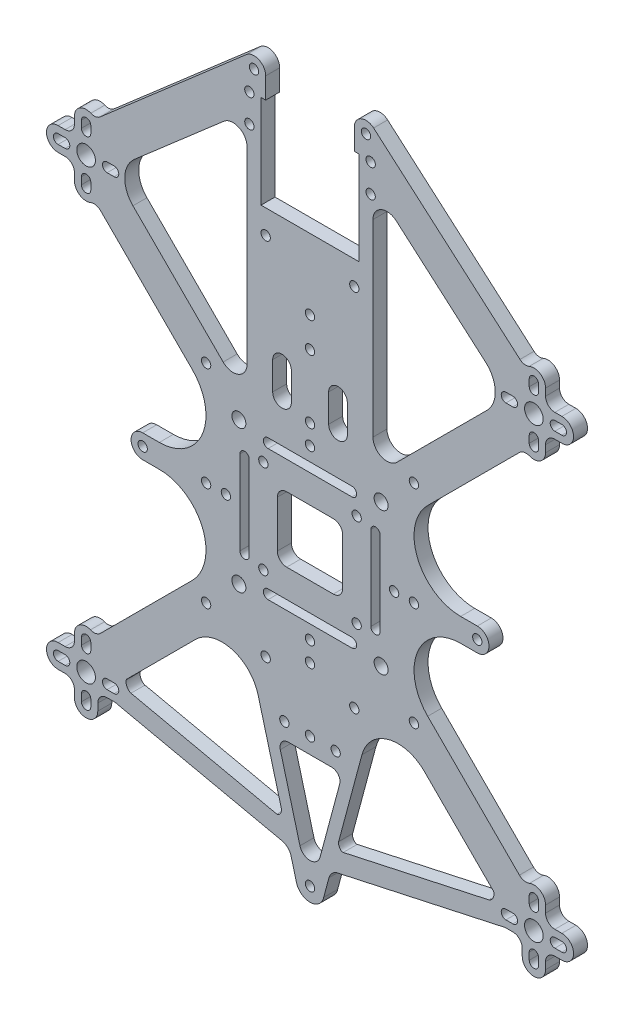
SolidWorks part; units mm, degrees
ref_plane "前视基准面" through (0, 0, 0) normal (0, 0, 1) x (1, 0, 0)
ref_plane "上视基准面" through (0, 0, 0) normal (0, 1, 0) x (1, 0, 0)
ref_plane "右视基准面" through (0, 0, 0) normal (1, 0, 0) x (0, 0, -1)
sketch "Model" plane through (0, 0, 0) normal (0, 0, 1) x (1, 0, 0)
  line L0 (38.9722, 86.626) -> (42.5374, 86.626)
  line L1 (49.6078, 103.6978) -> (29.9424, 123.3592)
  line L2 (37.1859, 136.508) -> (56.373, 153.1829)
  line L3 (61.3409, 150.9185) -> (61.3409, 110.5212)
  line L4 (56.2198, 108.3997) -> (36.8794, 127.7362)
  line L5 (27.8409, 136.6164) -> (27.8409, 138.1164)
  line L6 (25.8409, 138.1164) -> (25.8409, 136.6164)
  line L7 (27.8409, 127.6164) -> (27.8409, 126.1164)
  line L8 (25.8409, 126.1164) -> (25.8409, 127.6164)
  line L9 (22.3409, 133.1164) -> (20.8409, 133.1164)
  line L10 (20.8409, 131.1164) -> (22.3409, 131.1164)
  line L11 (31.3409, 133.1164) -> (32.8409, 133.1164)
  line L12 (32.8409, 131.1164) -> (31.3409, 131.1164)
  line L13 (24.3409, 126.1164) -> (24.3409, 127.6164)
  line L14 (22.3409, 129.6164) -> (20.8409, 129.6164)
  line L15 (20.8409, 134.6164) -> (22.3409, 134.6164)
  line L16 (24.3409, 136.6164) -> (24.3409, 138.1164)
  line L17 (27.8409, 31.6356) -> (27.8409, 30.1356)
  line L18 (25.8409, 30.1356) -> (25.8409, 31.6356)
  line L19 (27.8409, 40.6356) -> (27.8409, 42.1356)
  line L20 (25.8409, 42.1356) -> (25.8409, 40.6356)
  line L21 (22.3409, 35.1356) -> (20.8409, 35.1356)
  line L22 (20.8409, 37.1356) -> (22.3409, 37.1356)
  line L23 (31.3409, 35.1356) -> (32.8409, 35.1356)
  line L24 (32.8409, 37.1356) -> (31.3409, 37.1356)
  line L25 (121.8409, 31.6356) -> (121.8409, 30.1356)
  line L26 (123.8409, 30.1356) -> (123.8409, 31.6356)
  line L27 (121.8409, 40.6356) -> (121.8409, 42.1356)
  line L28 (123.8409, 42.1356) -> (123.8409, 40.6356)
  line L29 (127.3409, 35.1356) -> (128.8409, 35.1356)
  line L30 (128.8409, 37.1356) -> (127.3409, 37.1356)
  line L31 (118.3409, 35.1356) -> (116.8409, 35.1356)
  line L32 (116.8409, 37.1356) -> (118.3409, 37.1356)
  line L33 (125.3409, 42.1356) -> (125.3409, 40.6356)
  line L34 (127.3409, 38.6356) -> (128.8409, 38.6356)
  line L35 (128.8409, 33.6356) -> (127.3409, 33.6356)
  line L36 (125.3409, 31.6356) -> (125.3409, 30.1356)
  line L37 (120.3409, 30.1356) -> (120.3409, 31.6356)
  line L38 (118.3409, 33.6356) -> (116.8409, 33.6356)
  line L39 (65.3409, 166.0907) -> (65.3409, 161.5907)
  line L40 (65.3409, 161.5907) -> (64.3409, 161.5907)
  line L41 (64.3409, 161.5907) -> (64.3409, 141.5907)
  line L42 (64.3409, 141.5907) -> (74.8409, 141.5907)
  line L43 (29.8244, 140.7093) -> (61.2009, 167.9777)
  line L44 (84.3409, 166.0907) -> (84.3409, 161.5907)
  line L45 (84.3409, 161.5907) -> (85.3409, 161.5907)
  line L46 (85.3409, 161.5907) -> (85.3409, 141.5907)
  line L47 (85.3409, 141.5907) -> (74.8409, 141.5907)
  line L48 (114.0826, 39.2358) -> (99.3617, 53.9538)
  line L49 (85.978, 50.3669) -> (80.98, 31.728)
  line L50 (81.2114, 42.5628) -> (76.9926, 26.8183)
  line L51 (72.6891, 26.8183) -> (68.4704, 42.5628)
  line L52 (70.1918, 44.8062) -> (79.4899, 44.8062)
  line L53 (110.7096, 81.626) -> (107.1443, 81.626)
  line L54 (100.074, 64.5542) -> (119.7393, 44.8928)
  line L55 (110.7096, 86.626) -> (107.1443, 86.626)
  line L56 (100.074, 103.6978) -> (119.7393, 123.3592)
  line L57 (121.8409, 136.6164) -> (121.8409, 138.1164)
  line L58 (123.8409, 138.1164) -> (123.8409, 136.6164)
  line L59 (121.8409, 127.6164) -> (121.8409, 126.1164)
  line L60 (123.8409, 126.1164) -> (123.8409, 127.6164)
  line L61 (127.3409, 133.1164) -> (128.8409, 133.1164)
  line L62 (128.8409, 131.1164) -> (127.3409, 131.1164)
  line L63 (118.3409, 133.1164) -> (116.8409, 133.1164)
  line L64 (116.8409, 131.1164) -> (118.3409, 131.1164)
  line L65 (125.3409, 126.1164) -> (125.3409, 127.6164)
  line L66 (127.3409, 129.6164) -> (128.8409, 129.6164)
  line L67 (128.8409, 134.6164) -> (127.3409, 134.6164)
  line L68 (125.3409, 136.6164) -> (125.3409, 138.1164)
  line L69 (119.8573, 140.7093) -> (88.4808, 167.9777)
  line L70 (112.4959, 136.508) -> (93.3088, 153.1829)
  line L71 (88.3409, 150.9185) -> (88.3409, 110.5212)
  line L72 (93.462, 108.3997) -> (112.8023, 127.7362)
  line L73 (61.8096, 93.126) -> (61.8096, 75.126)
  line L74 (59.8096, 75.126) -> (59.8096, 93.126)
  line L75 (69.8409, 91.126) -> (79.8409, 91.126)
  line L76 (81.8409, 89.126) -> (81.8409, 79.126)
  line L77 (79.8409, 77.126) -> (69.8409, 77.126)
  line L78 (67.8409, 79.126) -> (67.8409, 89.126)
  line L79 (87.8721, 93.126) -> (87.8721, 75.126)
  line L80 (89.8721, 75.126) -> (89.8721, 93.126)
  line L81 (65.8409, 71.0948) -> (83.8409, 71.0948)
  line L82 (83.8409, 69.0948) -> (65.8409, 69.0948)
  line L83 (65.8409, 97.1572) -> (83.8409, 97.1572)
  line L84 (83.8409, 99.1572) -> (65.8409, 99.1572)
  line L85 (70.8409, 114.1572) -> (70.8409, 108.1572)
  line L86 (66.8409, 108.1572) -> (66.8409, 114.1572)
  line L87 (78.8409, 114.1572) -> (78.8409, 108.1572)
  line L88 (82.8409, 108.1572) -> (82.8409, 114.1572)
  line L89 (80.7239, 25.7968) -> (115.3738, 33.3482)
  line L90 (77.7722, 19.7649) -> (78.9081, 24.001)
  line L91 (81.9571, 30.2136) -> (113.2232, 37.0275)
  line L92 (24.3409, 42.1356) -> (24.3409, 40.6356)
  line L93 (22.3409, 38.6356) -> (20.8409, 38.6356)
  line L94 (20.8409, 33.6356) -> (22.3409, 33.6356)
  line L95 (24.3409, 31.6356) -> (24.3409, 30.1356)
  line L96 (29.3409, 30.1356) -> (29.3409, 31.6356)
  line L97 (31.3409, 33.6356) -> (32.8409, 33.6356)
  line L98 (68.9578, 25.7968) -> (34.3079, 33.3482)
  line L99 (71.926, 19.6934) -> (70.7737, 24.001)
  line L100 (38.9722, 81.626) -> (42.5374, 81.626)
  line L101 (49.6078, 64.5542) -> (29.9424, 44.8928)
  line L102 (35.5991, 39.2358) -> (50.32, 53.9538)
  line L103 (63.7037, 50.3669) -> (68.7017, 31.728)
  line L104 (67.7246, 30.2136) -> (36.4585, 37.0275)
  circle A0 centre (97.1147, 106.3999) radius 1
  circle A1 centre (52.567, 106.3999) radius 1
  circle A2 centre (52.567, 61.8522) radius 1
  circle A3 centre (97.1147, 61.8522) radius 1
  circle A4 centre (97.1147, 84.126) radius 1
  circle A5 centre (74.8409, 106.3999) radius 1
  circle A6 centre (52.567, 84.126) radius 1
  circle A7 centre (74.8409, 61.8522) radius 1
  circle A8 centre (64.8409, 94.126) radius 1
  circle A9 centre (84.8409, 94.126) radius 1
  circle A10 centre (64.8409, 74.126) radius 1
  circle A11 centre (84.8409, 74.126) radius 1
  circle A12 centre (26.8409, 132.1164) radius 2
  circle A13 centre (74.8409, 102.1572) radius 1
  circle A14 centre (92.8721, 84.126) radius 1
  circle A15 centre (74.8409, 66.0948) radius 1
  circle A16 centre (56.8096, 84.126) radius 1
  arc A17 (110.7096, 81.626) -> (110.7096, 86.626) centre (110.7096, 84.126) ccw
  circle A18 centre (110.7096, 84.126) radius 1
  arc A19 (38.9722, 86.626) -> (38.9722, 81.626) centre (38.9722, 84.126) ccw
  circle A20 centre (38.9722, 84.126) radius 1
  circle A21 centre (74.8409, 120.0231) radius 1
  circle A22 centre (74.8409, 48.229) radius 1
  circle A23 centre (26.8409, 36.1356) radius 2
  circle A24 centre (122.8409, 36.1356) radius 2
  arc A25 (65.3409, 166.0907) -> (61.2009, 167.9777) centre (62.8409, 166.0907) ccw
  circle A26 centre (62.8409, 166.0907) radius 1
  arc A27 (88.4808, 167.9777) -> (84.3409, 166.0907) centre (86.8409, 166.0907) ccw
  circle A28 centre (86.8409, 166.0907) radius 1
  circle A29 centre (74.8409, 20.4032) radius 1
  arc A30 (71.926, 19.6934) -> (77.7722, 19.7649) centre (74.8409, 20.4032) ccw
  arc A31 (119.7393, 44.8928) -> (121.9034, 44.4531) centre (121.1534, 46.3072) ccw
  arc A32 (27.7784, 44.4531) -> (29.9424, 44.8928) centre (28.5284, 46.3072) ccw
  arc A33 (29.9424, 123.3592) -> (27.7784, 123.7989) centre (28.5284, 121.9448) ccw
  arc A34 (27.843, 140.4068) -> (29.8244, 140.7093) centre (28.5945, 142.1245) ccw
  arc A35 (37.1859, 136.508) -> (36.8794, 127.7362) centre (41.1216, 131.9792) ccw
  circle A36 centre (122.8409, 132.1164) radius 2
  arc A37 (121.9034, 123.7989) -> (119.7393, 123.3592) centre (121.1534, 121.9448) ccw
  arc A38 (119.8573, 140.7093) -> (121.8388, 140.4068) centre (121.0872, 142.1245) ccw
  arc A39 (112.8023, 127.7362) -> (112.4959, 136.508) centre (108.5601, 131.9792) ccw
  circle A40 centre (65.3409, 136.4775) radius 1
  circle A41 centre (84.3409, 136.4775) radius 1
  circle A42 centre (90.0909, 99.376) radius 1.5
  circle A43 centre (59.5909, 99.376) radius 1.5
  circle A44 centre (90.0909, 68.876) radius 1.5
  circle A45 centre (59.5909, 68.876) radius 1.5
  circle A46 centre (87.8409, 161.3753) radius 1
  circle A47 centre (87.8409, 155.3753) radius 1
  circle A48 centre (61.8409, 161.3753) radius 1
  circle A49 centre (61.8409, 155.3753) radius 1
  circle A50 centre (74.8409, 126.4775) radius 1
  circle A51 centre (65.3409, 58.229) radius 1
  circle A52 centre (84.3409, 58.229) radius 1
  circle A53 centre (80.3409, 48.229) radius 1
  circle A54 centre (69.3409, 48.229) radius 1
  arc A55 (42.5374, 86.626) -> (49.6078, 103.6978) centre (42.5374, 96.626) ccw
  arc A56 (61.3409, 150.9185) -> (56.373, 153.1829) centre (58.3409, 150.9185) ccw
  arc A57 (56.2198, 108.3997) -> (61.3409, 110.5212) centre (58.3409, 110.5212) ccw
  arc A58 (27.8409, 138.1164) -> (25.8409, 138.1164) centre (26.8409, 138.1164) ccw
  arc A59 (25.8409, 136.6164) -> (27.8409, 136.6164) centre (26.8409, 136.6164) ccw
  arc A60 (25.8409, 126.1164) -> (27.8409, 126.1164) centre (26.8409, 126.1164) ccw
  arc A61 (27.8409, 127.6164) -> (25.8409, 127.6164) centre (26.8409, 127.6164) ccw
  arc A62 (20.8409, 133.1164) -> (20.8409, 131.1164) centre (20.8409, 132.1164) ccw
  arc A63 (22.3409, 131.1164) -> (22.3409, 133.1164) centre (22.3409, 132.1164) ccw
  arc A64 (32.8409, 131.1164) -> (32.8409, 133.1164) centre (32.8409, 132.1164) ccw
  arc A65 (31.3409, 133.1164) -> (31.3409, 131.1164) centre (31.3409, 132.1164) ccw
  arc A66 (24.3409, 126.1164) -> (27.7784, 123.7989) centre (26.8409, 126.1164) ccw
  arc A67 (24.3409, 127.6164) -> (22.3409, 129.6164) centre (22.3409, 127.6164) ccw
  arc A68 (20.8409, 134.6164) -> (20.8409, 129.6164) centre (20.8409, 132.1164) ccw
  arc A69 (22.3409, 134.6164) -> (24.3409, 136.6164) centre (22.3409, 136.6164) ccw
  arc A70 (27.843, 140.4068) -> (24.3409, 138.1164) centre (26.8409, 138.1164) ccw
  arc A71 (25.8409, 30.1356) -> (27.8409, 30.1356) centre (26.8409, 30.1356) ccw
  arc A72 (27.8409, 31.6356) -> (25.8409, 31.6356) centre (26.8409, 31.6356) ccw
  arc A73 (27.8409, 42.1356) -> (25.8409, 42.1356) centre (26.8409, 42.1356) ccw
  arc A74 (25.8409, 40.6356) -> (27.8409, 40.6356) centre (26.8409, 40.6356) ccw
  arc A75 (20.8409, 37.1356) -> (20.8409, 35.1356) centre (20.8409, 36.1356) ccw
  arc A76 (22.3409, 35.1356) -> (22.3409, 37.1356) centre (22.3409, 36.1356) ccw
  arc A77 (32.8409, 35.1356) -> (32.8409, 37.1356) centre (32.8409, 36.1356) ccw
  arc A78 (31.3409, 37.1356) -> (31.3409, 35.1356) centre (31.3409, 36.1356) ccw
  arc A79 (121.8409, 30.1356) -> (123.8409, 30.1356) centre (122.8409, 30.1356) ccw
  arc A80 (123.8409, 31.6356) -> (121.8409, 31.6356) centre (122.8409, 31.6356) ccw
  arc A81 (123.8409, 42.1356) -> (121.8409, 42.1356) centre (122.8409, 42.1356) ccw
  arc A82 (121.8409, 40.6356) -> (123.8409, 40.6356) centre (122.8409, 40.6356) ccw
  arc A83 (128.8409, 35.1356) -> (128.8409, 37.1356) centre (128.8409, 36.1356) ccw
  arc A84 (127.3409, 37.1356) -> (127.3409, 35.1356) centre (127.3409, 36.1356) ccw
  arc A85 (116.8409, 37.1356) -> (116.8409, 35.1356) centre (116.8409, 36.1356) ccw
  arc A86 (118.3409, 35.1356) -> (118.3409, 37.1356) centre (118.3409, 36.1356) ccw
  arc A87 (125.3409, 42.1356) -> (121.9034, 44.4531) centre (122.8409, 42.1356) ccw
  arc A88 (125.3409, 40.6356) -> (127.3409, 38.6356) centre (127.3409, 40.6356) ccw
  arc A89 (128.8409, 33.6356) -> (128.8409, 38.6356) centre (128.8409, 36.1356) ccw
  arc A90 (127.3409, 33.6356) -> (125.3409, 31.6356) centre (127.3409, 31.6356) ccw
  arc A91 (120.3409, 30.1356) -> (125.3409, 30.1356) centre (122.8409, 30.1356) ccw
  arc A92 (120.3409, 31.6356) -> (118.3409, 33.6356) centre (118.3409, 31.6356) ccw
  arc A93 (99.3617, 53.9538) -> (85.978, 50.3669) centre (93.7054, 48.2963) ccw
  arc A94 (72.6891, 26.8183) -> (76.9926, 26.8183) centre (74.8409, 27.3948) ccw
  arc A95 (70.1918, 44.8062) -> (68.4704, 42.5628) centre (70.1918, 43.024) ccw
  arc A96 (81.2114, 42.5628) -> (79.4899, 44.8062) centre (79.4899, 43.024) ccw
  arc A97 (107.1443, 81.626) -> (100.074, 64.5542) centre (107.1443, 71.626) ccw
  arc A98 (100.074, 103.6978) -> (107.1443, 86.626) centre (107.1443, 96.626) ccw
  arc A99 (123.8409, 138.1164) -> (121.8409, 138.1164) centre (122.8409, 138.1164) ccw
  arc A100 (121.8409, 136.6164) -> (123.8409, 136.6164) centre (122.8409, 136.6164) ccw
  arc A101 (121.8409, 126.1164) -> (123.8409, 126.1164) centre (122.8409, 126.1164) ccw
  arc A102 (123.8409, 127.6164) -> (121.8409, 127.6164) centre (122.8409, 127.6164) ccw
  arc A103 (128.8409, 131.1164) -> (128.8409, 133.1164) centre (128.8409, 132.1164) ccw
  arc A104 (127.3409, 133.1164) -> (127.3409, 131.1164) centre (127.3409, 132.1164) ccw
  arc A105 (116.8409, 133.1164) -> (116.8409, 131.1164) centre (116.8409, 132.1164) ccw
  arc A106 (118.3409, 131.1164) -> (118.3409, 133.1164) centre (118.3409, 132.1164) ccw
  arc A107 (121.9034, 123.7989) -> (125.3409, 126.1164) centre (122.8409, 126.1164) ccw
  arc A108 (127.3409, 129.6164) -> (125.3409, 127.6164) centre (127.3409, 127.6164) ccw
  arc A109 (128.8409, 129.6164) -> (128.8409, 134.6164) centre (128.8409, 132.1164) ccw
  arc A110 (125.3409, 136.6164) -> (127.3409, 134.6164) centre (127.3409, 136.6164) ccw
  arc A111 (125.3409, 138.1164) -> (121.8388, 140.4068) centre (122.8409, 138.1164) ccw
  arc A112 (93.3088, 153.1829) -> (88.3409, 150.9185) centre (91.3409, 150.9185) ccw
  arc A113 (88.3409, 110.5212) -> (93.462, 108.3997) centre (91.3409, 110.5212) ccw
  arc A114 (61.8096, 93.126) -> (60.8096, 94.126) centre (60.8096, 93.126) ccw
  arc A115 (59.8096, 75.126) -> (61.8096, 75.126) centre (60.8096, 75.126) ccw
  arc A116 (60.8096, 94.126) -> (59.8096, 93.126) centre (60.8096, 93.126) ccw
  arc A117 (81.8409, 89.126) -> (79.8409, 91.126) centre (79.8409, 89.126) ccw
  arc A118 (79.8409, 77.126) -> (81.8409, 79.126) centre (79.8409, 79.126) ccw
  arc A119 (67.8409, 79.126) -> (69.8409, 77.126) centre (69.8409, 79.126) ccw
  arc A120 (69.8409, 91.126) -> (67.8409, 89.126) centre (69.8409, 89.126) ccw
  arc A121 (88.8721, 94.126) -> (87.8721, 93.126) centre (88.8721, 93.126) ccw
  arc A122 (87.8721, 75.126) -> (89.8721, 75.126) centre (88.8721, 75.126) ccw
  arc A123 (89.8721, 93.126) -> (88.8721, 94.126) centre (88.8721, 93.126) ccw
  arc A124 (65.8409, 71.0948) -> (64.8409, 70.0948) centre (65.8409, 70.0948) ccw
  arc A125 (83.8409, 69.0948) -> (83.8409, 71.0948) centre (83.8409, 70.0948) ccw
  arc A126 (64.8409, 70.0948) -> (65.8409, 69.0948) centre (65.8409, 70.0948) ccw
  arc A127 (64.8409, 98.1572) -> (65.8409, 97.1572) centre (65.8409, 98.1572) ccw
  arc A128 (83.8409, 97.1572) -> (83.8409, 99.1572) centre (83.8409, 98.1572) ccw
  arc A129 (65.8409, 99.1572) -> (64.8409, 98.1572) centre (65.8409, 98.1572) ccw
  arc A130 (70.8409, 114.1572) -> (68.8409, 116.1572) centre (68.8409, 114.1572) ccw
  arc A131 (66.8409, 108.1572) -> (70.8409, 108.1572) centre (68.8409, 108.1572) ccw
  arc A132 (68.8409, 116.1572) -> (66.8409, 114.1572) centre (68.8409, 114.1572) ccw
  arc A133 (80.8409, 116.1572) -> (78.8409, 114.1572) centre (80.8409, 114.1572) ccw
  arc A134 (78.8409, 108.1572) -> (82.8409, 108.1572) centre (80.8409, 108.1572) ccw
  arc A135 (82.8409, 114.1572) -> (80.8409, 116.1572) centre (80.8409, 114.1572) ccw
  arc A136 (27.7784, 44.4531) -> (24.3409, 42.1356) centre (26.8409, 42.1356) ccw
  arc A137 (22.3409, 38.6356) -> (24.3409, 40.6356) centre (22.3409, 40.6356) ccw
  arc A138 (20.8409, 38.6356) -> (20.8409, 33.6356) centre (20.8409, 36.1356) ccw
  arc A139 (24.3409, 31.6356) -> (22.3409, 33.6356) centre (22.3409, 31.6356) ccw
  arc A140 (24.3409, 30.1356) -> (29.3409, 30.1356) centre (26.8409, 30.1356) ccw
  arc A141 (31.3409, 33.6356) -> (29.3409, 31.6356) centre (31.3409, 31.6356) ccw
  arc A142 (49.6078, 64.5542) -> (42.5374, 81.626) centre (42.5374, 71.626) ccw
  arc A143 (63.7037, 50.3669) -> (50.32, 53.9538) centre (55.9763, 48.2963) ccw
  spline S0 degree 3 poles (-99.7214, -129.1915) (-99.388, -129.1915) (-99.0547, -129.1915) (-98.7214, -129.1915) knots 0 0 0 0 1 1 1 1
  spline S1 degree 3 poles (-99.7214, -129.1915) (-99.388, -129.1915) (-99.0547, -129.1915) (-98.7214, -129.1915) knots 0 0 0 0 1 1 1 1
  spline S2 degree 3 poles (80.98, 31.728) (80.8244, 31.1477) (81.3701, 30.0856) (81.9571, 30.2136) knots 0 0 0 0 1.802262 1.802262 1.802262 1.802262
  spline S3 degree 3 poles (114.0826, 39.2358) (114.6412, 38.6773) (113.995, 37.1957) (113.2232, 37.0275) knots 0 0 0 0 2.369586 2.369586 2.369586 2.369586
  spline S4 degree 3 poles (80.7239, 25.7968) (79.8921, 25.6155) (79.1285, 24.8232) (78.9081, 24.001) knots 0 0 0 0 2.553871 2.553871 2.553871 2.553871
  spline S5 degree 3 poles (116.8409, 33.6356) (116.3426, 33.6356) (115.8607, 33.4543) (115.3738, 33.3482) knots 0 0 0 0 1.494916 1.494916 1.494916 1.494916
  spline S6 degree 3 poles (68.9578, 25.7968) (69.7896, 25.6155) (70.5532, 24.8232) (70.7737, 24.001) knots 0 0 0 0 2.553871 2.553871 2.553871 2.553871
  spline S7 degree 3 poles (32.8409, 33.6356) (33.3392, 33.6356) (33.821, 33.4543) (34.3079, 33.3482) knots 0 0 0 0 1.494916 1.494916 1.494916 1.494916
  spline S8 degree 3 poles (68.7017, 31.728) (68.8573, 31.1477) (68.3116, 30.0856) (67.7246, 30.2136) knots 0 0 0 0 1.802262 1.802262 1.802262 1.802262
  spline S9 degree 3 poles (35.5991, 39.2358) (35.0405, 38.6773) (35.6868, 37.1957) (36.4585, 37.0275) knots 0 0 0 0 2.369586 2.369586 2.369586 2.369586
extrude "凸台-拉伸1" add sketch "Model" along normal blind 3 contours S0 S1 | L63 A105 L64 A106 | L61 A103 L62 A104 | L48 A93 L49 S2 L91 S3 | A6 | A5 | A4 | A3 | A2 | A1 | A0 | L102 A143 L103 S8 L104 S9 | L73 A115 L74 A116 A114 | A14 | A13 | A12 | A11 | A10 | A9 | A8 | A7 | L75 A117 L76 A118 L77 A119 L78 A120 | A22 | A21 | A20 | A18 | A16 | A15 | L83 A128 L84 A129 A127 | L81 A125 L82 A126 A124 | L79 A122 L80 A123 A121 | L0 A55 L1 A33 A66 L13 A67 L14 A68 L15 A69 L16 A70 A34 L43 A25 L39 L40 L41 L42 L47 L46 L45 L44 A27 L69 A38 A111 L68 A110 L67 A109 L66 A108 L65 A107 A37 L56 A98 L55 A17 L53 A97 L54 A31 A87 L33 A88 L34 A89 L35 A90 L36 A91 L37 A92 L38 S5 L89 S4 L90 A30 L99 S6 L98 S7 L97 A141 L96 A140 L95 A139 L94 A138 L93 A137 L92 A136 A32 L101 A142 L100 A19 | A29 | A28 | A26 | A24 | A23 | L87 A134 L88 A135 A133 | L85 A131 L86 A132 A130 | L2 A56 L3 A57 L4 A35 | A42 | A41 | A40 | A36 | L70 A112 L71 A113 L72 A39 | A50 | A49 | A48 | A47 | A46 | A45 | A44 | A43 | A54 | A53 | A52 | A51 | L7 A60 L8 A61 | L5 A58 L6 A59 | L11 A64 L12 A65 | L9 A62 L10 A63 | L19 A73 L20 A74 | L17 A71 L18 A72 | L23 A77 L24 A78 | L21 A75 L22 A76 | L29 A83 L30 A84 | L27 A81 L28 A82 | L25 A79 L26 A80 | L31 A85 L32 A86 | L50 A94 L51 A95 L52 A96 | L59 A101 L60 A102 | L57 A99 L58 A100
